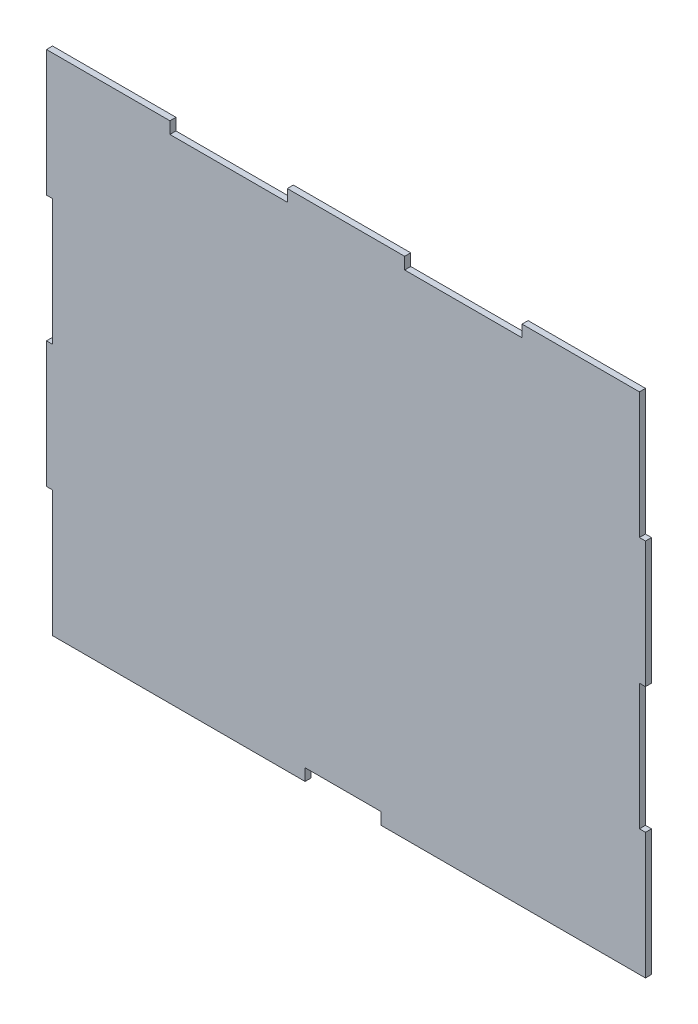
SolidWorks part; units mm, degrees
material "Acrylic (Medium-high impact)"
ref_plane "Front Plane" through (0, 0, 0) normal (0, 0, 1) x (1, 0, 0)
ref_plane "Top Plane" through (0, 0, 0) normal (0, 1, 0) x (1, 0, 0)
ref_plane "Right Plane" through (0, 0, 0) normal (1, 0, 0) x (0, 0, -1)
sketch "Sketch1" plane through (0, 0, 0) normal (0, 0, 1) x (1, 0, 0)
  line L0 (127.127, 0) -> (127.127, 5.9944)
  line L1 (0, 0) -> (127.127, 0)
  line L2 (-3.048, 63.5) -> (-3.048, 127)
  line L3 (-3.048, 253.9817) -> (59.0804, 253.9817)
  line L4 (298.45, 0) -> (298.45, 63.5)
  line L5 (127.127, 5.9944) -> (165.227, 5.9944)
  line L6 (165.227, 5.9944) -> (165.227, 0)
  line L7 (0, 0) -> (0, 63.5)
  line L8 (0, 63.5) -> (-3.048, 63.5)
  line L9 (0, 127) -> (-3.048, 127)
  line L10 (0, 127) -> (0, 190.5)
  line L11 (0, 190.5) -> (-3.048, 190.5)
  line L12 (-3.048, 190.5) -> (-3.048, 253.9817)
  line L13 (165.227, 0) -> (298.45, 0)
  line L14 (59.0804, 253.9817) -> (59.0804, 248.0127)
  line L15 (59.0804, 248.0127) -> (118.1608, 248.0127)
  line L16 (118.1608, 248.0127) -> (118.1608, 253.9817)
  line L17 (177.2412, 253.9817) -> (177.2412, 248.0127)
  line L18 (177.2412, 248.0127) -> (236.3216, 248.0127)
  line L19 (236.3216, 248.0127) -> (236.3216, 253.9817)
  line L20 (118.1608, 253.9817) -> (177.2412, 253.9817)
  line L21 (236.3216, 253.9817) -> (295.402, 253.9817)
  line L22 (298.45, 63.5) -> (295.402, 63.5)
  line L23 (295.402, 63.5) -> (295.402, 126.9817)
  line L24 (295.402, 126.9817) -> (298.45, 126.9817)
  line L25 (298.45, 190.4817) -> (295.402, 190.4817)
  line L26 (295.402, 190.4817) -> (295.402, 253.9817)
  line L29 (298.45, 126.9817) -> (298.45, 190.4817)
  dimension "D1" = 254
  dimension "D2" = 298.45
  dimension "D3" = 5.9944
  dimension "D4" = 38.1
  dimension "D5" = 130.175
  dimension "D6" = 63.5
  dimension "D7" = 3.048
  dimension "D8" = 5.969
  dimension "D9" = 59.0804
  dimension "D10" = 3.048
extrude "Boss-Extrude1" add sketch "Sketch1" along normal blind 3.048
